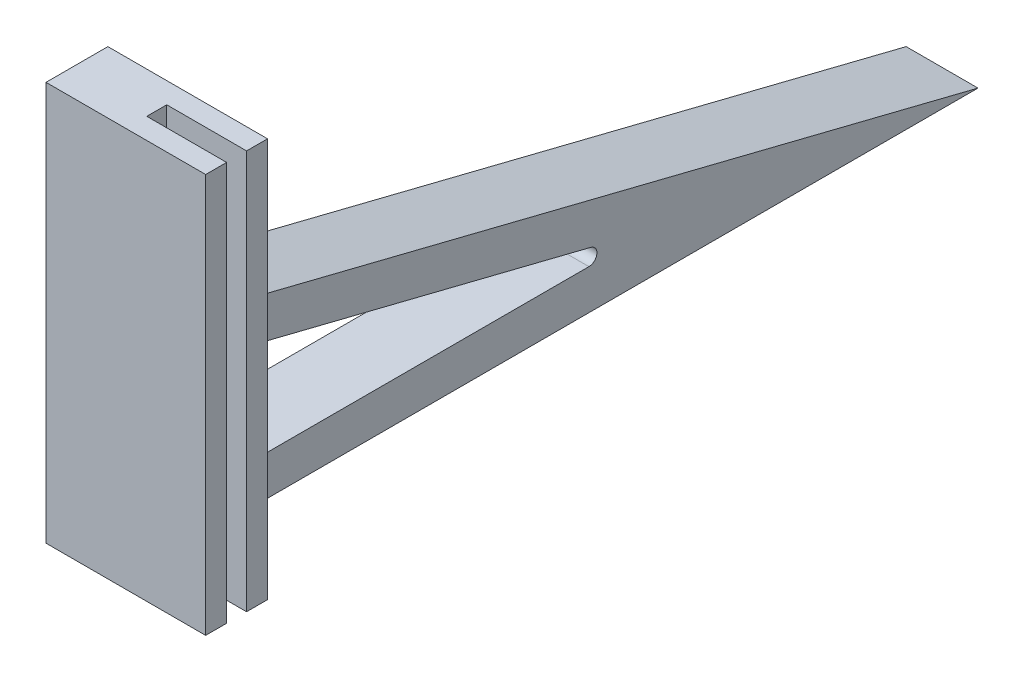
SolidWorks part; units mm, degrees
ref_plane "Front Plane" through (0, 0, 0) normal (0, 0, 1) x (1, 0, 0)
ref_plane "Top Plane" through (0, 0, 0) normal (0, 1, 0) x (1, 0, 0)
ref_plane "Right Plane" through (0, 0, 0) normal (1, 0, 0) x (0, 0, -1)
sketch "Sketch1" plane through (0, 0, 0) normal (0, 1, 0) x (1, 0, 0)
  line L0 (0, 0) -> (20, 0)
  line L1 (0, 0) -> (0, 5)
  line L2 (0, 5) -> (20, 5)
  line L3 (20, 5) -> (20, 10.25)
  line L4 (20, 0) -> (20, -5.25)
  line L5 (20, -5.25) -> (-20, -5.25)
  line L6 (-20, -5.25) -> (-20, 10.25)
  line L7 (20, 10.25) -> (-20, 10.25)
  dimension "D1" = 20
  dimension "D2" = 5
  dimension "D3" = 5.25
  dimension "D4" = 5.25
  dimension "D5" = 40
  dimension "D6" = 40
extrude "Boss-Extrude1" add sketch "Sketch1" along normal blind 100
sketch "Sketch2" plane through (-20, 0, 0) normal (-1, 0, 0) x (0, 0, 1)
  line L0 (-10.25, 0) -> (-210.25, 0)
  line L1 (-210.25, 0) -> (-10.25, 50)
  line L2 (-10.25, 100) -> (-10.25, 0) construction
  dimension "D1" = 200
extrude "Extrude-Thin1" add sketch "Sketch2" against normal blind 18 thin
fillet "Fillet1" radius 3 1 edges at (-11, 50, -10.25)
fillet "Fillet2" radius 3 1 edges at (-11, 10, -10.25)
fillet "Fillet3" radius 2 1 edges at (-11, 39.6922, -10.25)
fillet "Fillet4" radius 2 1 edges at (-11, 10, -129.0189)
sketch "Sketch3" plane through (0, 0, -10.25) normal (0, 0, -1) x (-1, 0, 0)
  line L0 (-1020, 50) -> (48980, 50) construction
  line L1 (-20, 100) -> (-20, 0) construction
  line L2 (-10, -950) -> (-10, 49050) construction
  circle A0 centre (-10, 50) radius 2.5
  point P5 (-20, 50)
  dimension "D1" = 10
extrude "Cut-Extrude1" cut sketch "Sketch3" against normal up to next
